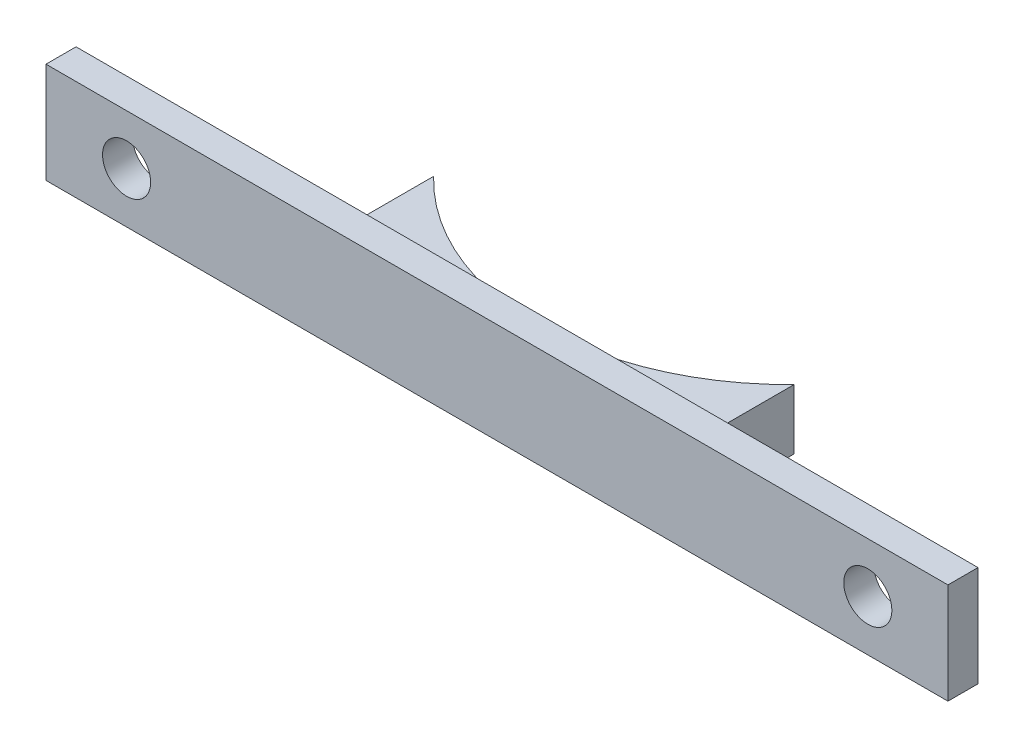
SolidWorks part; units mm, degrees
ref_plane "Front Plane" through (0, 0, 0) normal (0, 0, 1) x (1, 0, 0)
ref_plane "Top Plane" through (0, 0, 0) normal (0, 1, 0) x (1, 0, 0)
ref_plane "Right Plane" through (0, 0, 0) normal (1, 0, 0) x (0, 0, -1)
sketch "Sketch2" plane through (0, 0, 0) normal (0, 0, 1) x (1, 0, 0)
  line L2 (-31.75, 0) -> (-31.75, 31.75)
  line L3 (-31.75, 31.75) -> (31.75, 31.75)
  line L4 (31.75, 31.75) -> (31.75, 0)
  line L5 (31.75, 0) -> (31.75, -31.75)
  line L6 (31.75, -31.75) -> (-31.75, -31.75)
  line L7 (-31.75, -31.75) -> (-31.75, 0)
  line L8 (-31.75, 0) -> (-46.99, 0)
  line L9 (31.75, 0) -> (46.99, 0)
  line L10 (-57.2066, 0) -> (-57.2066, 6.35)
  line L11 (-57.2066, 6.35) -> (-31.75, 6.35)
  line L12 (-57.2066, 0) -> (-57.2066, -6.4183)
  line L13 (-57.2066, -6.4183) -> (57.15, -6.4183)
  line L14 (57.15, -6.4183) -> (57.15, 0)
  line L15 (57.15, 6.35) -> (-31.75, 6.35)
  line L16 (57.15, 0) -> (57.15, 6.35)
  circle A0 centre (-46.99, 0) radius 3.048
  circle A1 centre (46.99, 0) radius 3.048
sketch "Sketch3" plane through (0, 0, 0) normal (0, 1, 0) x (1, 0, 0)
  line L0 (31.75, 0) -> (-31.75, 0)
  line L1 (31.75, 0) -> (-31.75, 0) construction
  line L2 (-57.2066, 0) -> (57.15, 0) construction
  line L5 (0, 0) -> (31.75, 0)
  line L7 (22.86, 10.9863) -> (22.86, 0)
  line L9 (-22.86, 10.9863) -> (-22.86, 0)
  arc A0 (-22.86, 10.9863) -> (22.86, 10.9863) centre (0, 33.02) ccw
extrude "Boss-Extrude1" add sketch "Sketch2" along normal blind 3.81
extrude "Boss-Extrude2" add sketch "Sketch3" along normal blind 3.81 and the other way blind 3.81 contours A0 L9 L0 L5 L7
